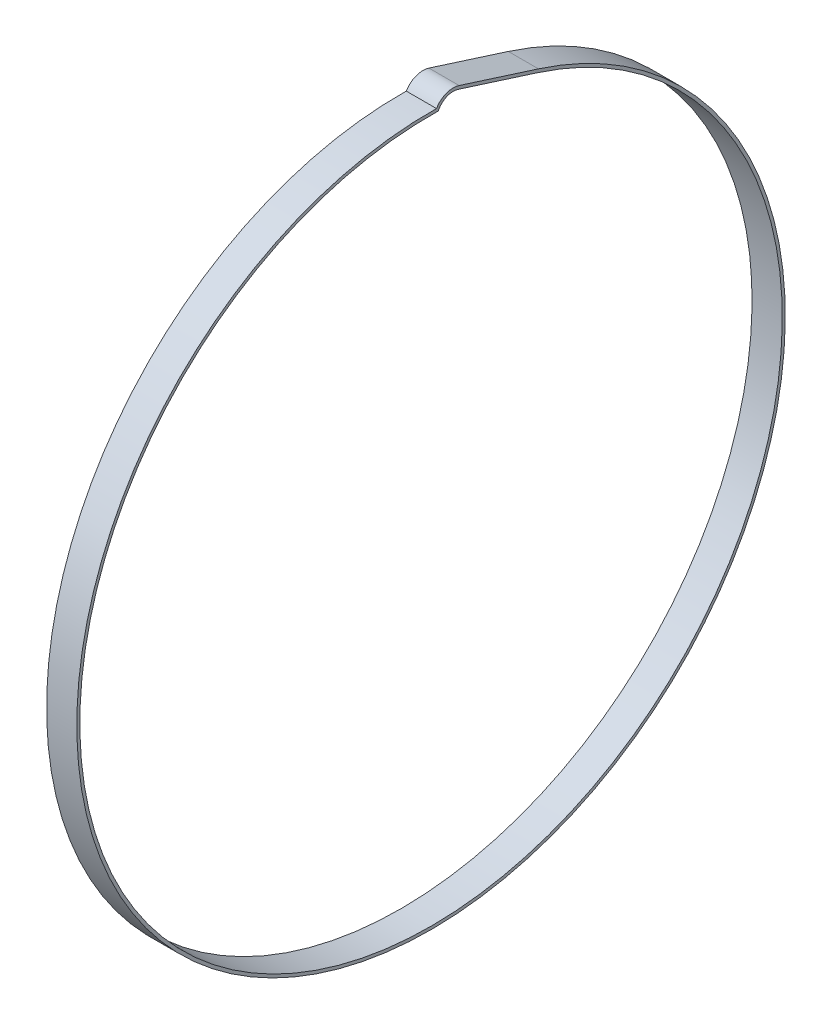
SolidWorks part; units mm, degrees
ref_plane "Front Plane" through (0, 0, 0) normal (0, 0, 1) x (1, 0, 0)
ref_plane "Top Plane" through (0, 0, 0) normal (0, 1, 0) x (1, 0, 0)
ref_plane "Right Plane" through (0, 0, 0) normal (1, 0, 0) x (0, 0, -1)
sketch "Sketch1" plane through (0, 0, 0) normal (1, 0, 0) x (0, 0, -1)
  line L0 (0, 0) -> (0, 204.895) construction
  line L2 (45.1725, 141.957) -> (11.797, 152.5776)
  line L3 (44.7874, 140.7468) -> (11.4119, 151.3674)
  arc A0 (3.0395, 147.6697) -> (44.7874, 140.7468) centre (0, 0) ccw
  arc A2 (11.4119, 151.3674) -> (3.0395, 147.6697) centre (9.3169, 144.7836) ccw
  arc A5 (2.2806, 148.9535) -> (45.1725, 141.957) centre (0, 0) ccw
  arc A6 (11.797, 152.5776) -> (2.2806, 148.9535) centre (9.3169, 144.7836) ccw
  point P3 (0, 0)
  dimension "D1" = 295.402
  dimension "D2" = 1.27
extrude "Boss-Extrude1" add sketch "Sketch1" along normal blind 12.7
